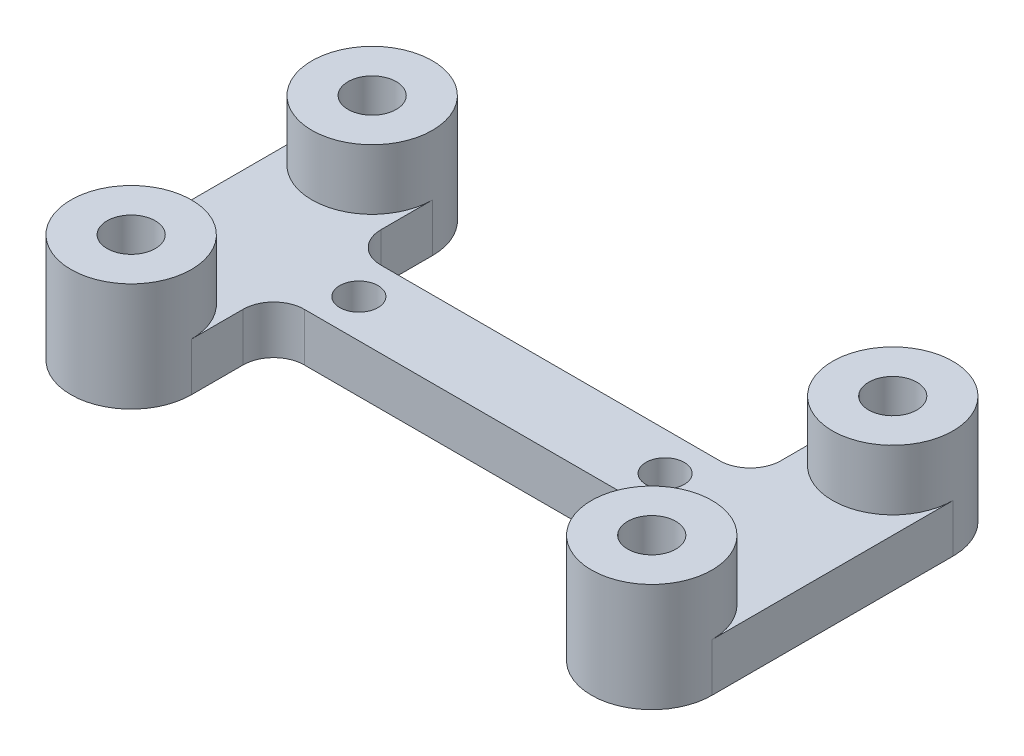
SolidWorks part; units mm, degrees
ref_plane "Front Plane" through (0, 0, 0) normal (0, 0, 1) x (1, 0, 0)
ref_plane "Top Plane" through (0, 0, 0) normal (0, 1, 0) x (1, 0, 0)
ref_plane "Right Plane" through (0, 0, 0) normal (1, 0, 0) x (0, 0, -1)
sketch "Sketch4" plane through (0, 0, 0) normal (0, 1, 0) x (1, 0, 0)
  line L1 (-21.59, -9.9949) -> (21.59, -9.9949) construction
  line L2 (-21.59, -9.9949) -> (-21.59, 9.9949) construction
  line L3 (-21.59, 9.9949) -> (21.59, 9.9949) construction
  line L4 (21.59, -9.9949) -> (21.59, 9.9949) construction
  line L5 (-21.59, -9.9949) -> (21.59, 9.9949) construction
  line L6 (-21.59, 9.9949) -> (21.59, -9.9949) construction
  circle A0 centre (-21.59, 9.9949) radius 5
  circle A1 centre (-21.59, -9.9949) radius 5
  circle A2 centre (21.59, 9.9949) radius 5
  circle A3 centre (21.59, -9.9949) radius 5
  circle A4 centre (21.59, -9.9949) radius 2
  circle A5 centre (21.59, 9.9949) radius 2
  circle A6 centre (-21.59, -9.9949) radius 2
  circle A7 centre (-21.59, 9.9949) radius 2
  point P0 (0, 0)
  dimension "D3" = 4
  dimension "D4" = 10
  dimension "D5" = 4
  dimension "D6" = 10
  dimension "D7" = 4
  dimension "D8" = 10
  dimension "D9" = 10
  dimension "D10" = 4
  dimension "D1" = 19.9898
  dimension "D2" = 43.18
extrude "Boss-Extrude3" add sketch "Sketch4" along normal blind 9
sketch "Sketch5" plane through (0, 0, 0) normal (0, 1, 0) x (1, 0, 0)
  line L1 (-26.59, -9.9949) -> (-16.59, -9.9949)
  line L2 (-26.59, -9.9949) -> (-26.59, 9.9949)
  line L3 (-26.59, 9.9949) -> (-16.59, 9.9949)
  line L4 (-16.59, -9.9949) -> (-16.59, 9.9949)
  line L5 (-26.59, -9.9949) -> (-16.59, 9.9949) construction
  line L6 (-26.59, 9.9949) -> (-16.59, -9.9949) construction
  line L7 (0, -3.175) -> (-16.59, -3.175)
  line L8 (0, -3.175) -> (0, 3.175)
  line L9 (0, 3.175) -> (-16.59, 3.175)
  line L10 (-16.59, -3.175) -> (-16.59, 3.175)
  line L11 (0, -3.175) -> (-16.59, 3.175) construction
  line L12 (0, 3.175) -> (-16.59, -3.175) construction
  circle A0 centre (-21.59, 9.9949) radius 5 construction
  circle A1 centre (-21.59, 9.9949) radius 2
  circle A2 centre (-21.59, -9.9949) radius 2
  point P0 (-21.59, 0)
  point P9 (-8.295, 0)
  dimension "D1" = 6.35
extrude "Boss-Extrude4" add sketch "Sketch5" along normal blind 4 contours L1 L4 L3 L2 | L8 L9 L4 L7
mirror "Mirror1" about plane through (0, 0, 0) normal (1, 0, 0) of "Boss-Extrude4"
sketch "Sketch6" plane through (0, 4, 0) normal (0, 1, 0) x (1, 0, 0)
  line L0 (-12.7, 0) -> (12.7, 0) construction
  circle A0 centre (-12.7, 0) radius 1.5875
  circle A1 centre (12.7, 0) radius 1.5875
  dimension "D2" = 3.175
  dimension "D3" = 3.175
  dimension "D1" = 25.4
extrude "Cut-Extrude1" cut sketch "Sketch6" against normal through all
fillet "Fillet1" radius 2.54 4 edges at (16.59, 2, 3.175) (16.59, 2, -3.175) (-16.59, 2, -3.175) (-16.59, 2, 3.175)
